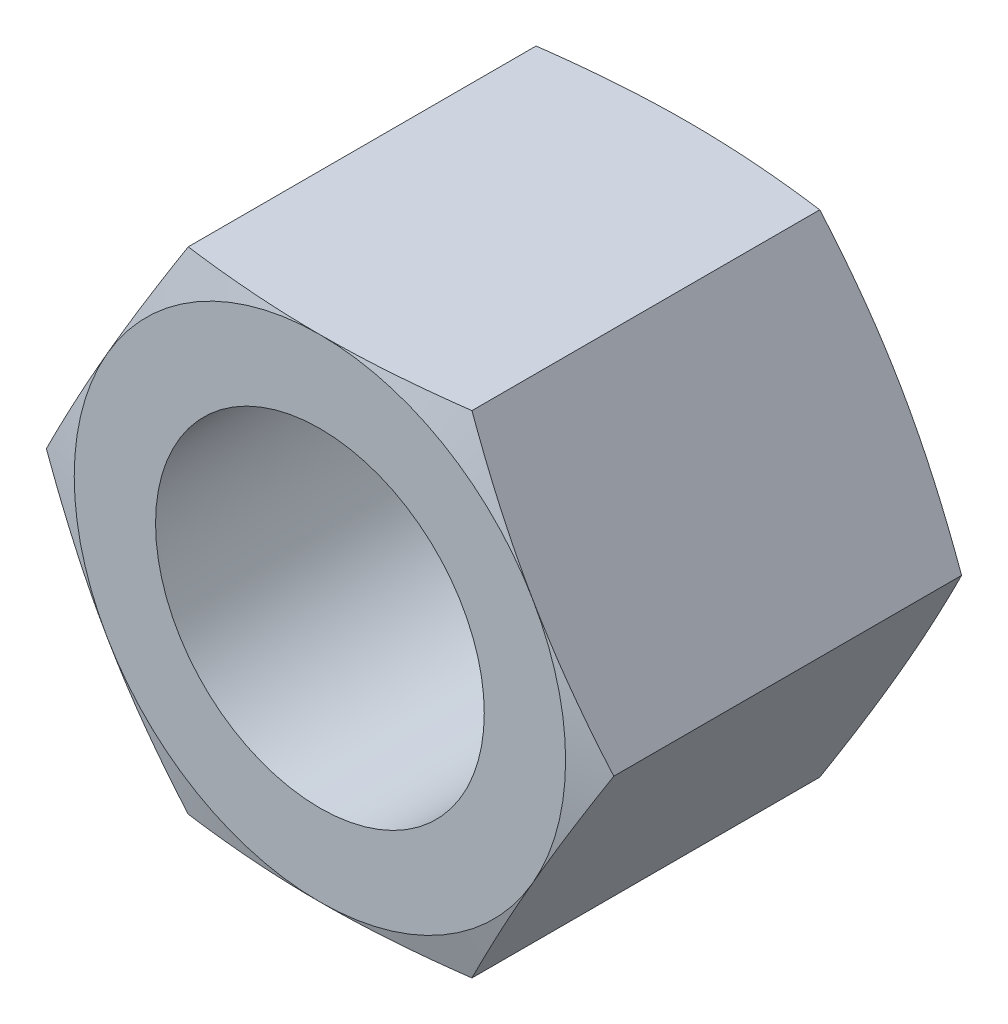
SolidWorks part; units mm, degrees
material "4级"
ref_plane "基准面1" through (0, 0, 0) normal (0, 0, 1) x (1, 0, 0)
ref_plane "基准面2" through (0, 0, 0) normal (0, 1, 0) x (1, 0, 0)
ref_plane "基准面3" through (0, 0, 0) normal (1, 0, 0) x (0, 0, -1)
sketch "尺寸草图" plane through (0, 0, 0) normal (0, 0, 1) x (1, 0, 0)
  line L0 (0, 0) -> (24.1005, 0)
  point P3 (5, 0)
  point P4 (1.5, 0)
  point P5 (8.63, 0)
  point P6 (5.6, 0)
  point P7 (6.4, 0)
  point P8 (8, 0)
  dimension "D" = 5
  dimension "P1" = 1.5
  dimension "e" = 8.63
  dimension "m" = 5.6
  dimension "mw" = 6.4
  dimension "s" = 8
sketch "草图1" plane through (0, 0, 0) normal (0, 0, 1) x (1, 0, 0)
  line L0 (-26.8088, 0) -> (37.1748, 0) construction
  line L1 (0, 25.0215) -> (0, -25.0215) construction
  line L3 (2.1575, 3.7369) -> (-2.1575, 3.7369)
  line L4 (-2.1575, 3.7369) -> (-4.315, 0)
  line L5 (-4.315, 0) -> (-2.1575, -3.7369)
  line L6 (-2.1575, -3.7369) -> (2.1575, -3.7369)
  line L7 (2.1575, -3.7369) -> (4.315, 0)
  line L8 (4.315, 0) -> (2.1575, 3.7369)
  circle A0 centre (0, 0) radius 3.7369 construction
  circle A1 centre (0, 0) radius 2.5
  dimension "D" = 5
  dimension "e" = 8.63
extrude "基体-拉伸" add sketch "草图1" along normal blind 5.6
cosmetic thread "装饰螺纹线1" parameters "D2"=5.25
sketch "草图2" plane through (0, 0, 0) normal (0, 0, -1) x (-1, 0, 0)
  line L0 (-2.1575, 3.7369) -> (2.1575, 3.7369) construction
  circle A0 centre (0, 0) radius 3.7369
  circle A1 centre (0, 0) radius 2.5 construction
extrude "切除-拉伸1" cut sketch "草图2" against normal blind 38 draft 75 flip side to cut
sketch "草图3" plane through (0, 0, 5.6) normal (0, 0, 1) x (1, 0, 0)
  line L0 (4.315, 0) -> (2.1575, 3.7369) construction
  circle A0 centre (0, 0) radius 3.7369
extrude "切除-拉伸2" cut sketch "草图3" against normal blind 38 draft 75 flip side to cut
chamfer "倒角1" [suppressed] distance 0.2 angle 45
equation "\"e@草图1\" = \"e@尺寸草图\""
equation "\"D@草图1\" = \"D@尺寸草图\""
equation "\"m@基体-拉伸\" = \"m@尺寸草图\""
equation "\"D2@装饰螺纹线1\" = 1.05 * \"D@尺寸草图\""
